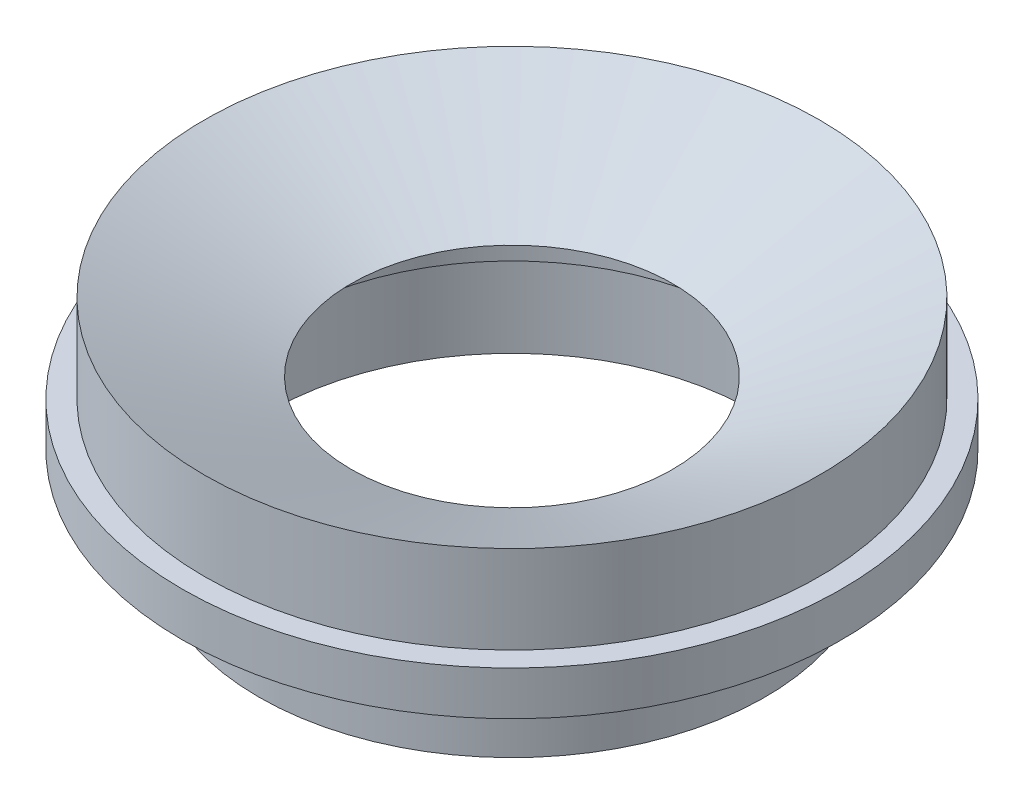
SolidWorks part; units mm, degrees
ref_plane "Front Plane" through (0, 0, 0) normal (0, 0, 1) x (1, 0, 0)
ref_plane "Top Plane" through (0, 0, 0) normal (0, 1, 0) x (1, 0, 0)
ref_plane "Right Plane" through (0, 0, 0) normal (1, 0, 0) x (0, 0, -1)
sketch "Sketch2" plane through (0, 0, 0) normal (0, 0, 1) x (1, 0, 0)
  line L0 (-32.3684, 31.1551) -> (-88.9, 57.5162)
  line L1 (-88.9, 57.5162) -> (-88.9, 32.1162)
  line L2 (-88.9, 32.1162) -> (-95.25, 32.1162)
  line L3 (-95.25, 32.1162) -> (-95.25, 19.4162)
  line L4 (-95.25, 19.4162) -> (-73.152, 19.4162)
  line L5 (-73.152, 19.4162) -> (-73.152, -105.7779)
  line L6 (-86.2301, -190.1338) -> (-28.9184, 23.7565)
  line L7 (-46.482, 37.7363) -> (-66.802, 37.7363)
  line L8 (-66.802, 37.7363) -> (-66.802, -5.9838)
  line L9 (-66.802, -5.9838) -> (-62.1491, -76.5637)
  line L10 (70.4832, 25.4) -> (-70.4683, 25.4) construction
  line L11 (0, 26.1547) -> (0, -177.6574) construction
  line L12 (-35.052, 41.271) -> (-35.052, -133.1831) construction
  line L13 (-95.25, 19.4162) -> (-95.25, 6.7162)
  line L14 (-95.25, 6.7162) -> (-82.55, 6.7162)
  line L15 (-82.55, 6.7162) -> (-82.55, -152.7009)
  line L16 (-62.1491, -76.5637) -> (-55.7991, -76.5637)
  line L17 (-28.702, 25.4) -> (-28.702, -128.0692) construction
  line L18 (-95.25, 0.7726) -> (-95.25, -56.7838)
  line L19 (-95.25, -56.7838) -> (-82.55, -56.7838)
  line L20 (-95.25, 0.7726) -> (-89.3064, 0.7726)
  line L21 (-89.3064, 0.7726) -> (-89.3064, 6.7162)
  line L22 (-73.152, -105.7779) -> (-63.627, -105.7779)
  line L23 (-92.5801, -190.1338) -> (-86.2301, -190.1338)
  line L24 (-82.55, -152.7009) -> (-76.2, -152.7009)
  line L25 (-86.2301, -190.1338) -> (-92.5801, -190.1338)
  line L26 (0, -56.7838) -> (-101.6, -56.7838) construction
  line L27 (-101.6, -56.7838) -> (-92.5801, -190.1338)
  line L28 (-101.6, -56.7838) -> (-95.25, -56.7838)
  line L29 (-69.977, 19.4162) -> (-69.977, -5.9498)
  line L30 (-69.977, -5.9498) -> (-73.152, -5.9498)
  line L31 (-69.977, 19.4162) -> (-66.802, 19.4162)
  arc A0 (-28.9184, 23.7565) -> (-32.3684, 31.1551) centre (-35.052, 25.4) ccw
  dimension "D3" = 12.7
  dimension "D1" = 25.4
  dimension "D2" = 12.7
  dimension "D4" = 114.3
  dimension "D5" = 6.35
  dimension "D6" = 6.35
  dimension "D7" = 95.25
  dimension "D8" = 15
  dimension "D9" = 25
  dimension "D10" = 28.702
  dimension "D11" = 12.7
  dimension "D12" = 6.35
  dimension "D13" = 44.45
  dimension "D14" = 25.4
  dimension "D15" = 63.5
  dimension "D16" = 12.7
  dimension "D17" = 5.9436
  dimension "D18" = 5.9436
  dimension "D19" = 9.525
  dimension "D20" = 101.6
  dimension "D21" = 6.35
  dimension "D22" = 133.35
  dimension "D23" = 6.35
  dimension "D24" = 20.32
  dimension "D25" = 25.4
  dimension "D26" = 3.175
  dimension "D27" = 25.366
revolve "Revolve1" add sketch "Sketch2" angle 360 about L11
